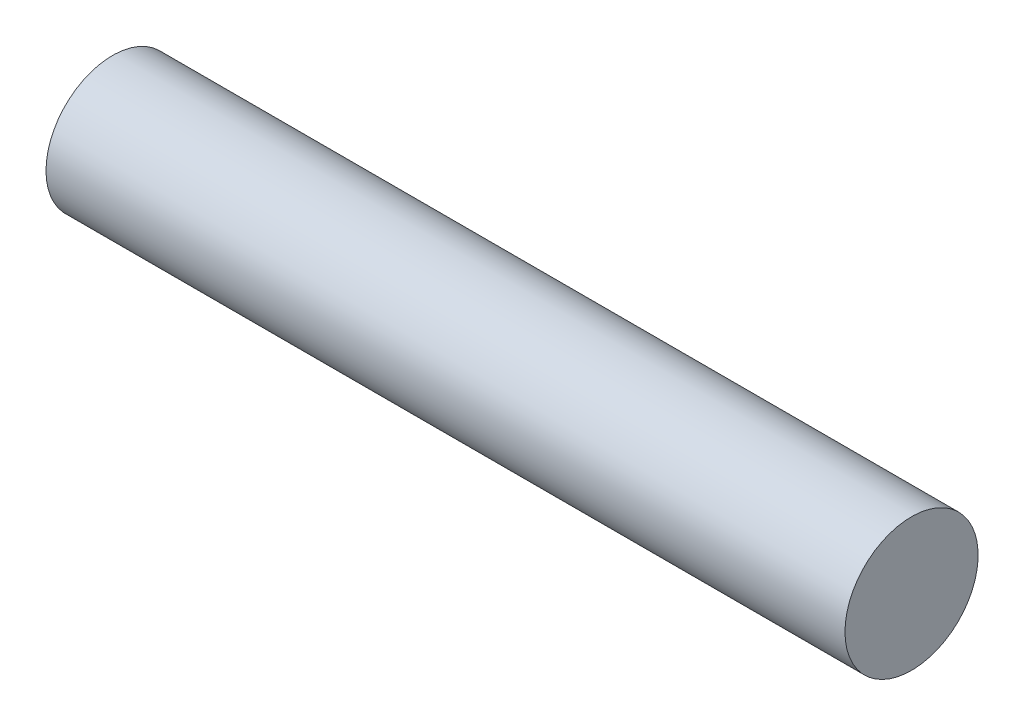
SolidWorks part; units mm, degrees
ref_plane "Front Plane" through (0, 0, 0) normal (0, 0, 1) x (1, 0, 0)
ref_plane "Top Plane" through (0, 0, 0) normal (0, 1, 0) x (1, 0, 0)
ref_plane "Right Plane" through (0, 0, 0) normal (1, 0, 0) x (0, 0, -1)
sketch "Sketch1" plane through (0, 0, 0) normal (0, 0, 1) x (1, 0, 0)
  line L0 (6, 44) -> (594, 44)
  line L2 (0, 44) -> (0, 50)
  line L3 (0, 50) -> (600, 50)
  line L4 (600, 0) -> (600, 50)
  line L8 (6, 44) -> (0, 44)
  line L9 (0, 0) -> (600, 0) construction
  line L10 (0, 0) -> (600, 0) construction
  line L11 (6, 6) -> (594, 6) construction
  line L12 (6, 6) -> (6, 44) construction
  line L13 (594, 44) -> (594, 0)
  line L14 (0, 0) -> (0, 50) construction
  line L15 (594, 6) -> (594, 44) construction
  line L16 (594, 0) -> (600, 0)
  dimension "D1" = 50
  dimension "D3" = 600
  dimension "D2" = 6
revolve "Revolve2" add sketch "Sketch1" angle 360 about L9
